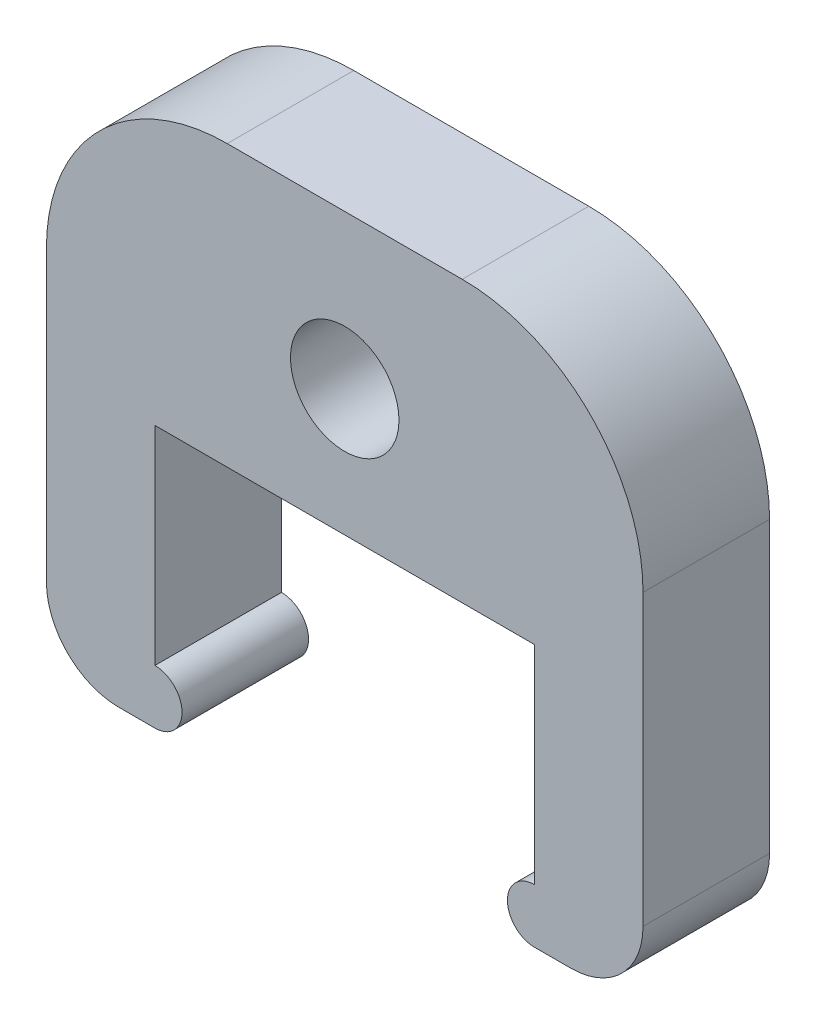
SolidWorks part; units mm, degrees
ref_plane "Front Plane" through (0, 0, 0) normal (0, 0, 1) x (1, 0, 0)
ref_plane "Top Plane" through (0, 0, 0) normal (0, 1, 0) x (1, 0, 0)
ref_plane "Right Plane" through (0, 0, 0) normal (1, 0, 0) x (0, 0, -1)
sketch "Sketch1" plane through (0, 0, 0) normal (0, 0, 1) x (1, 0, 0)
  line L0 (0, 15) -> (16.5, 15)
  line L1 (0, 0) -> (3, 0)
  line L2 (0, 0) -> (0, 15)
  line L4 (3, 1.5) -> (3, 7.25)
  line L7 (3, 7.25) -> (13.5, 7.25)
  line L10 (13.5, 7.25) -> (13.5, 1.5)
  line L11 (13.5, 0) -> (16.5, 0)
  line L12 (16.5, 15) -> (16.5, 0)
  arc A0 (3, 0) -> (3, 1.5) centre (3, 0.75) ccw
  arc A1 (13.5, 1.5) -> (13.5, 0) centre (13.5, 0.75) ccw
  circle A2 centre (8.25, 10.75) radius 1.5
  dimension "D5" = 1.5
  dimension "D6" = 1.5
  dimension "D7" = 3
  dimension "D8" = 3.5
  dimension "D1" = 15
  dimension "D2" = 7.25
  dimension "D3" = 10.5
  dimension "D4" = 3
extrude "Boss-Extrude1" add sketch "Sketch1" along normal blind 3.5
fillet "Fillet1" radius 2 2 edges at (16.5, 0, 1.75) (0, 0, 1.75)
fillet "Fillet2" radius 5 2 edges at (0, 15, 1.75) (16.5, 15, 1.75)
